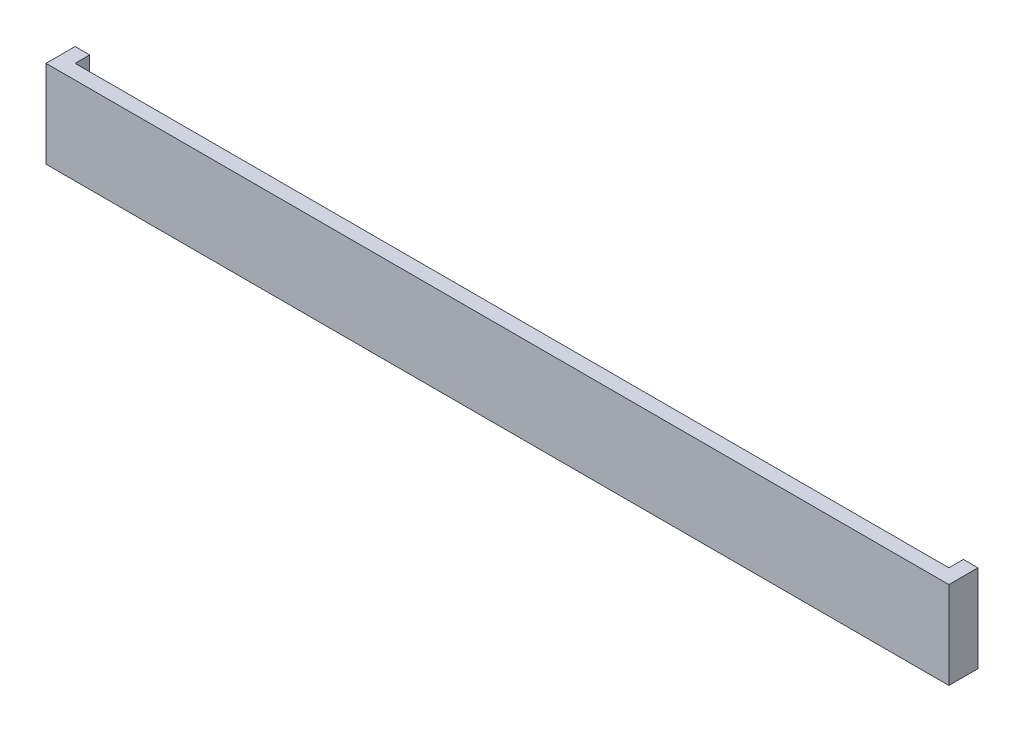
SolidWorks part; units mm, degrees
ref_plane "Front Plane" through (0, 0, 0) normal (0, 0, 1) x (1, 0, 0)
ref_plane "Top Plane" through (0, 0, 0) normal (0, 1, 0) x (1, 0, 0)
ref_plane "Right Plane" through (0, 0, 0) normal (1, 0, 0) x (0, 0, -1)
sketch "Sketch2" plane through (0, 0, 0) normal (0, 0, 1) x (1, 0, 0)
  line L1 (-310, -30) -> (310, -30)
  line L2 (-310, -30) -> (-310, 30)
  line L3 (-310, 30) -> (310, 30)
  line L4 (310, -30) -> (310, 30)
  line L5 (-310, -30) -> (310, 30) construction
  line L6 (-310, 30) -> (310, -30) construction
  point P0 (0, 0)
  dimension "D1" = 60
  dimension "D2" = 620
extrude "Boss-Extrude1" add sketch "Sketch2" along normal blind 20
sketch "Sketch4" plane through (0, 30, 0) normal (0, 1, 0) x (1, 0, 0)
  line L0 (310, 0) -> (-310, 0) construction
  line L1 (-300, 0) -> (300, 0)
  line L2 (-300, 0) -> (-300, -10)
  line L3 (-300, -10) -> (300, -10)
  line L4 (300, 0) -> (300, -10)
  line L5 (310, -20) -> (-310, -20) construction
  line L6 (310, -20) -> (310, 0) construction
  point P10 (0, -10)
  dimension "D1" = 10
  dimension "D2" = 10
extrude "Cut-Extrude1" cut sketch "Sketch4" against normal blind 100
